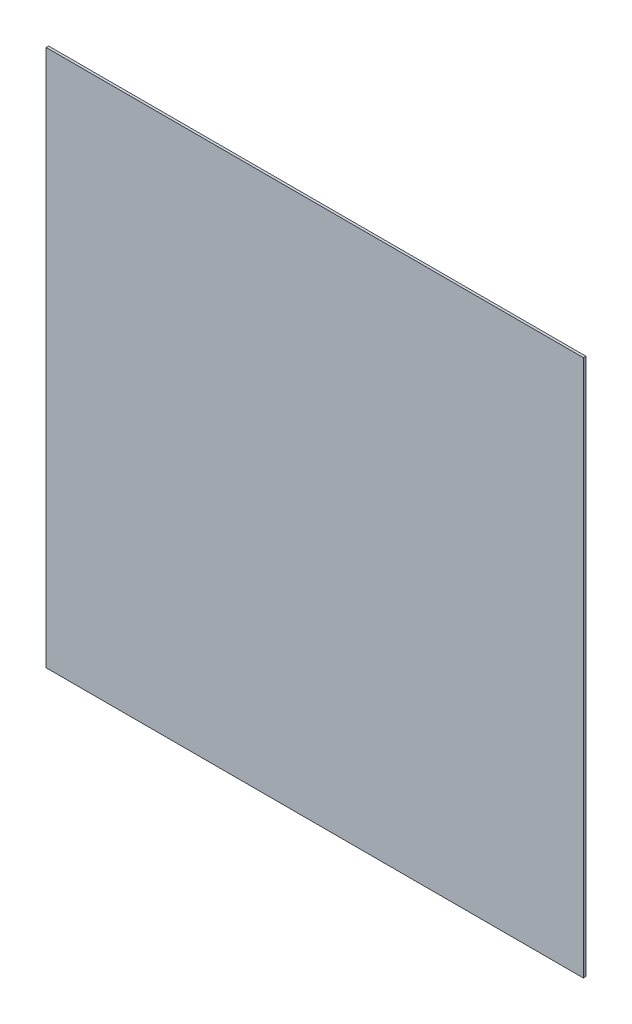
SolidWorks part; units mm, degrees
material "Verre"
ref_plane "Plan de face" through (0, 0, 0) normal (0, 0, 1) x (1, 0, 0)
ref_plane "Plan de dessus" through (0, 0, 0) normal (0, 1, 0) x (1, 0, 0)
ref_plane "Plan de droite" through (0, 0, 0) normal (1, 0, 0) x (0, 0, -1)
sketch "Esquisse1" plane through (0, 0, 0) normal (0, 0, 1) x (1, 0, 0)
  line L1 (0, 0) -> (-640, 0)
  line L2 (0, 0) -> (0, 640)
  line L3 (0, 640) -> (-640, 640)
  line L4 (-640, 0) -> (-640, 640)
  dimension "D1" = 640
extrude "Boss.-Extru.1" add sketch "Esquisse1" along normal blind 3
